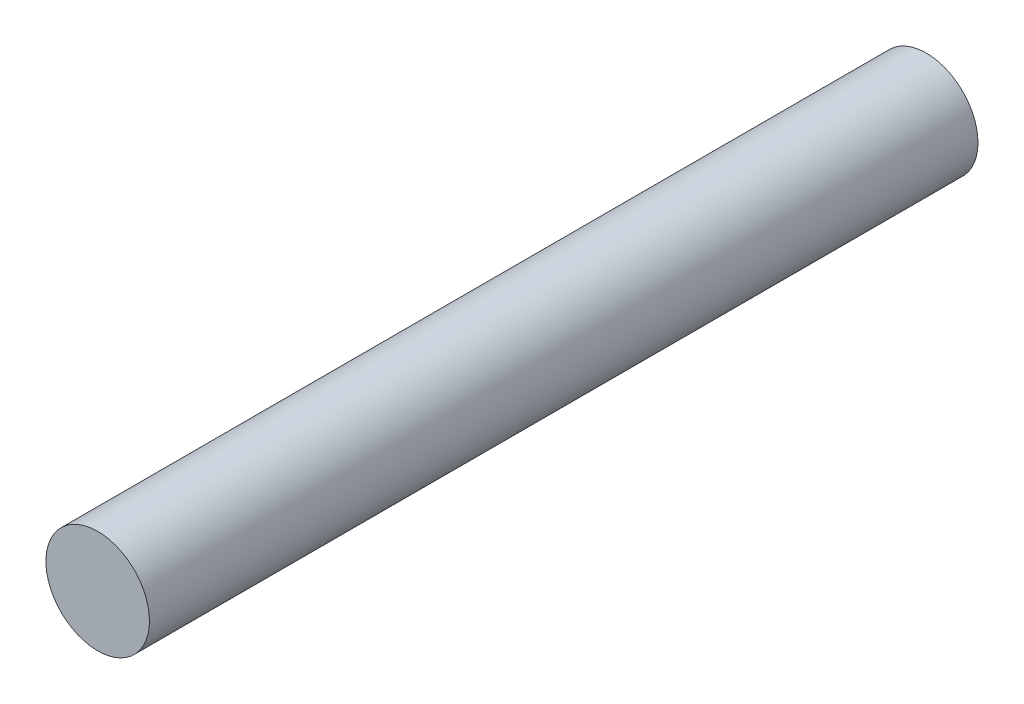
SolidWorks part; units mm, degrees
ref_plane "Front Plane" through (0, 0, 0) normal (0, 0, 1) x (1, 0, 0)
ref_plane "Top Plane" through (0, 0, 0) normal (0, 1, 0) x (1, 0, 0)
ref_plane "Right Plane" through (0, 0, 0) normal (1, 0, 0) x (0, 0, -1)
sketch "Sketch1" plane through (0, 0, 0) normal (0, 0, 1) x (1, 0, 0)
  circle A0 centre (0, 0) radius 6.35
  dimension "D1" = 12.7
extrude "Boss-Extrude1" add sketch "Sketch1" along normal blind 101.6
